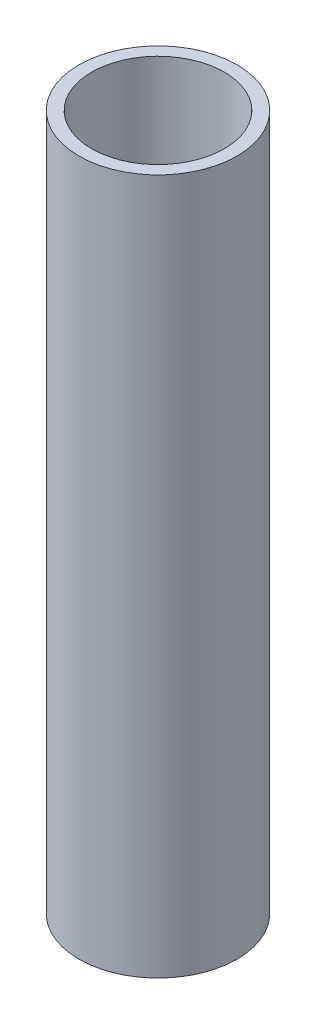
SolidWorks part; units mm, degrees
material "PVC 0.007 Plasticizado"
ref_plane "Plano frontal" through (0, 0, 0) normal (0, 0, 1) x (1, 0, 0)
ref_plane "Plano superior" through (0, 0, 0) normal (0, 1, 0) x (1, 0, 0)
ref_plane "Plano direito" through (0, 0, 0) normal (1, 0, 0) x (0, 0, -1)
sketch "Esboço3" plane through (0, 0, 0) normal (0, 0, 1) x (1, 0, 0)
  line L0 (10.5, 110) -> (12.5, 110)
  line L1 (12.5, 110) -> (12.5, 0)
  line L2 (12.5, 0) -> (3, 0)
  line L3 (3, 0) -> (3, 3)
  line L4 (3, 3) -> (8.5, 3)
  line L5 (8.5, 3) -> (8.5, 86)
  line L6 (8.5, 86) -> (10.5, 86)
  line L7 (10.5, 86) -> (10.5, 110)
  line L8 (0, 26.0213) -> (0, -109.8506) construction
  dimension "D1" = 25
  dimension "D2" = 110
  dimension "D3" = 21
  dimension "D4" = 6
  dimension "D5" = 3
  dimension "D6" = 24
revolve "Revolução1" add sketch "Esboço3" angle 360 about L8
